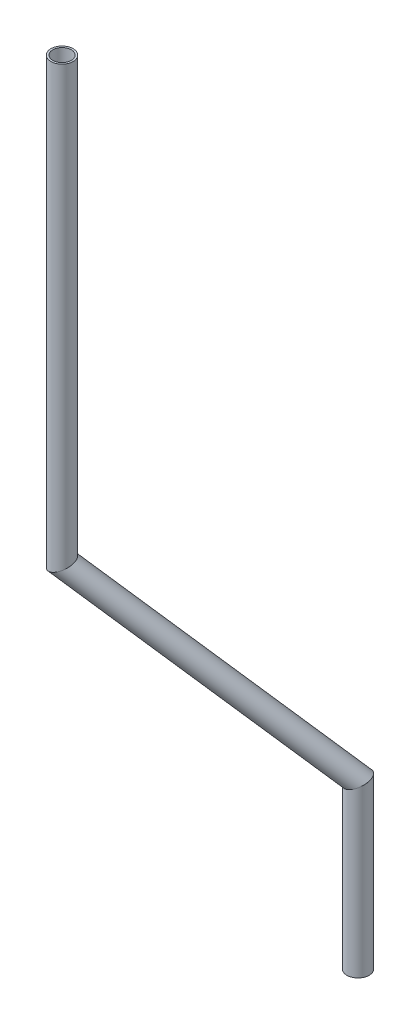
SolidWorks part; units mm, degrees
ref_plane "Front Plane" through (0, 0, 0) normal (0, 0, 1) x (1, 0, 0)
ref_plane "Top Plane" through (0, 0, 0) normal (0, 1, 0) x (1, 0, 0)
ref_plane "Right Plane" through (0, 0, 0) normal (1, 0, 0) x (0, 0, -1)
sketch3d "3DSketch1"
  line L0 (-436.1908, 824.6234, 450.4052) -> (-436.1908, 574.2119, 450.4052)
  line L1 (-436.1908, 574.2119, 450.4052) -> (-347.2745, 471.2598, 370.4181)
  line L2 (-347.2745, 471.2598, 370.4181) -> (-347.2745, 377.4661, 370.4181)
  circle A1 centre (-436.1908, 824.6234, 450.4052) radius 8.0124 construction
  point P5 (-436.1815, 816.611, 450.4365)
  point P9 (-419.3766, 523.4119, 429.5557)
other "Pipe 0.5 SCH 40(1)"
ref_plane "Plane1" through (-436.1908, 824.6234, 450.4052) normal (0, -1, 0) x (1, 0, 0)
sketch "Sketch1" plane through (-436.1908, 824.6234, 450.4052) normal (0, -1, 0) x (1, 0, 0)
  circle A0 centre (0, 0) radius 5.2832
  circle A1 centre (0, 0) radius 6.35
  point P5 (0, 0)
  dimension "In_dia" = 10.5664
  dimension "Out_dia" = 12.7
